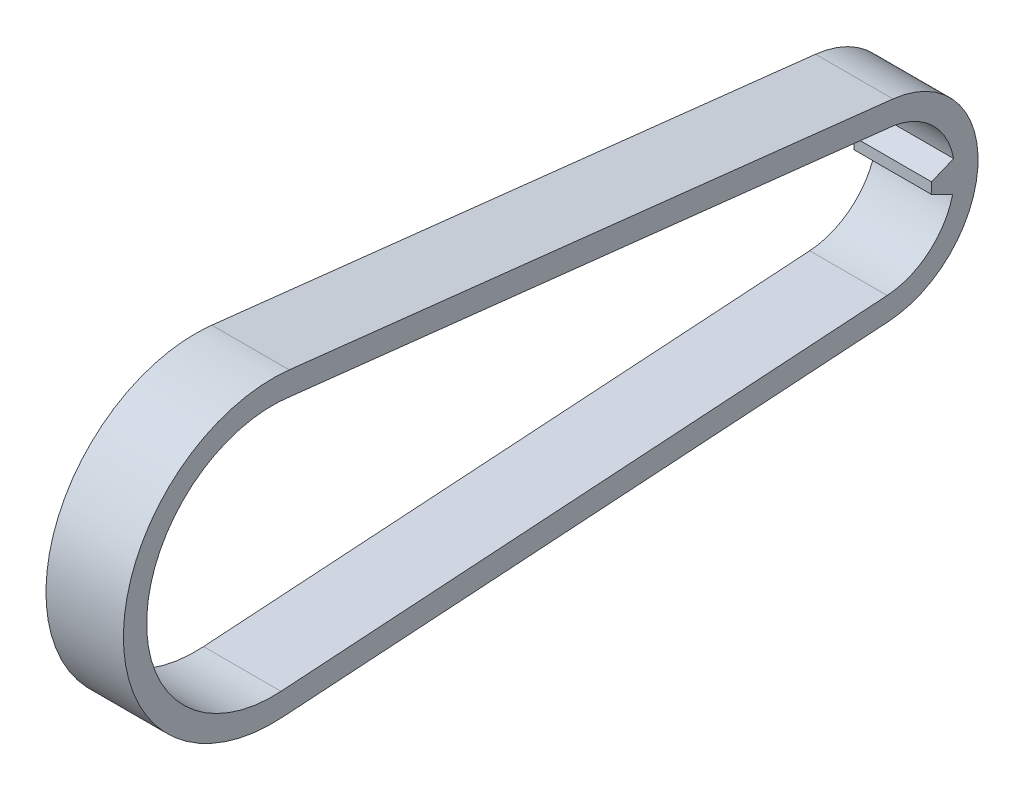
SolidWorks part; units mm, degrees
ref_plane "Front Plane" through (0, 0, 0) normal (0, 0, 1) x (1, 0, 0)
ref_plane "Top Plane" through (0, 0, 0) normal (0, 1, 0) x (1, 0, 0)
ref_plane "Right Plane" through (0, 0, 0) normal (1, 0, 0) x (0, 0, -1)
sketch "Sketch1" plane through (0, 0, 0) normal (1, 0, 0) x (0, 0, -1)
  line L0 (-76.5925, 20.9531) -> (1.3665, 12.2731)
  line L1 (-77.4657, -17.4501) -> (0.8072, -12.3225)
  line L2 (-77.6618, -14.4565) -> (0.6111, -9.3289)
  line L4 (-76.2165, 17.8769) -> (1.441, 9.2372)
  arc A0 (0.8072, -12.3225) -> (1.3665, 12.2731) centre (0, 0) ccw
  arc A1 (-76.5925, 20.9531) -> (-77.4657, -17.4501) centre (-78.7261, 1.7901) ccw
  arc A2 (-76.2165, 17.8769) -> (-77.6618, -14.4565) centre (-78.7261, 1.7901) ccw
  arc A3 (0.6111, -9.3289) -> (1.441, 9.2372) centre (0, 0) ccw
  circle A4 centre (-78.7261, 1.7901) radius 16.2814 construction
  circle A5 centre (0, 0) radius 9.3489 construction
  point P1 (0, 0)
  point P3 (0, 0)
  dimension "D1" = 3
  dimension "D2" = 3
extrude "Boss-Extrude1" add sketch "Sketch1" along normal blind 10
ref_plane "Plane1" through (0, 0, 0) normal (-1, 0, 0) x (0, 0, 1)
sketch "Sketch2" plane through (0, 0, 0) normal (-1, 0, 0) x (0, 0, 1)
  line L0 (-6.3367, 0.5185) -> (-9.1954, 1.6872)
  line L1 (-6.2992, -0.8619) -> (-9.069, -2.2705)
  line L2 (-6.3367, 0.5185) -> (-6.2992, -0.8619)
  arc A0 (-1.441, 9.2372) -> (-0.6111, -9.3289) centre (0, 0) ccw construction
  arc A1 (-9.069, -2.2705) -> (-9.1954, 1.6872) centre (0, 0) cw
extrude "Boss-Extrude2" add sketch "Sketch2" against normal blind 10
